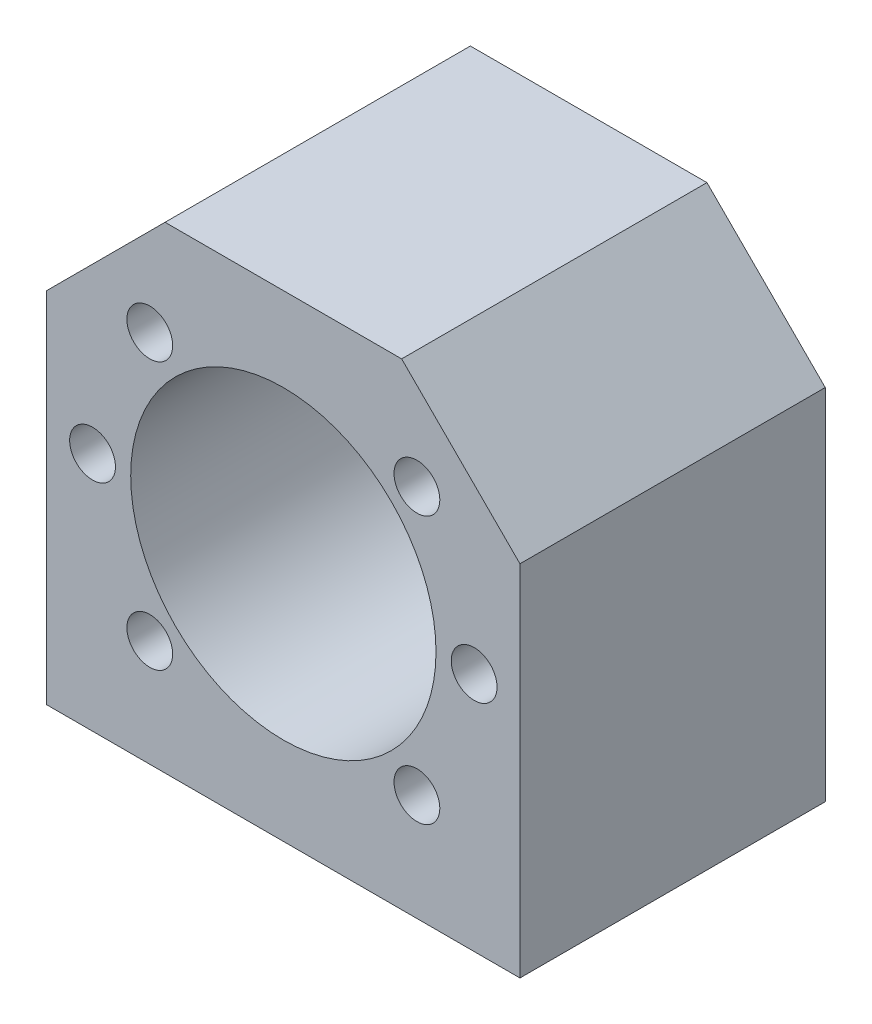
SolidWorks part; units mm, degrees
ref_plane "Płaszczyzna przednia" through (0, 0, 0) normal (0, 0, 1) x (1, 0, 0)
ref_plane "Płaszczyzna górna" through (0, 0, 0) normal (0, 1, 0) x (1, 0, 0)
ref_plane "Płaszczyzna prawa" through (0, 0, 0) normal (1, 0, 0) x (0, 0, -1)
sketch "Szkic1" plane through (0, 0, 0) normal (0, 0, 1) x (1, 0, 0)
  line L0 (31, -31.5) -> (31, 15.5)
  line L1 (31, 15.5) -> (15.5, 31)
  line L2 (15.5, 31) -> (-15.5, 31)
  line L3 (-15.5, 31) -> (-31, 15.5)
  line L4 (-31, 15.5) -> (-31, -31.5)
  line L10 (31, -31.5) -> (-31, -31.5)
  point P7 (0, 31)
  dimension "D1" = 31
  dimension "D2" = 135
  dimension "D3" = 135
  dimension "D4" = 62
  dimension "D5" = 47
  dimension "D6" = 31
extrude "Dodanie-wyciągnięcie1" add sketch "Szkic1" along normal blind 40
sketch "Szkic2" plane through (0, 0, 40) normal (0, 0, 1) x (1, 0, 0)
  circle A0 centre (0, 0) radius 20
  dimension "D1" = 40
extrude "Wytnij-wyciągnięcie1" cut sketch "Szkic2" against normal blind 40
sketch "Szkic4" plane through (0, 0, 40) normal (0, 0, 1) x (1, 0, 0)
  circle A0 centre (17.5, -17.5) radius 3
  circle A1 centre (25, 0) radius 3
  circle A2 centre (17.5, 17.5) radius 3
  circle A3 centre (-25, 0) radius 3
  circle A4 centre (-17.5, 17.5) radius 3
  circle A5 centre (-17.5, -17.5) radius 3
  dimension "D1" = 6
  dimension "D2" = 6
  dimension "D3" = 6
  dimension "D4" = 6
  dimension "D5" = 6
  dimension "D6" = 6
extrude "Wytnij-wyciągnięcie2" cut sketch "Szkic4" against normal blind 25
sketch "Szkic5" plane through (0, -31.5, 0) normal (0, -1, 0) x (1, 0, 0)
  line L0 (-31, 40) -> (-31, 0) construction
  line L1 (-31, 40) -> (31, 40) construction
  line L2 (-31, 0) -> (31, 0) construction
  line L3 (31, 40) -> (31, 0) construction
  circle A0 centre (-26, 33) radius 3
  circle A1 centre (-26, 7) radius 3
  circle A2 centre (26, 33) radius 3
  circle A3 centre (26, 7) radius 3
  point P8 (0, 0)
  point P9 (0, 0)
  point P10 (0, 0)
  point P11 (0, 0)
  point P12 (0, 0)
  dimension "D1" = 6
  dimension "D2" = 6
  dimension "D3" = 6
  dimension "D4" = 6
  dimension "D5" = 5
  dimension "D6" = 7
  dimension "D7" = 7
  dimension "D8" = 5
extrude "Wytnij-wyciągnięcie4" cut sketch "Szkic5" against normal blind 25
